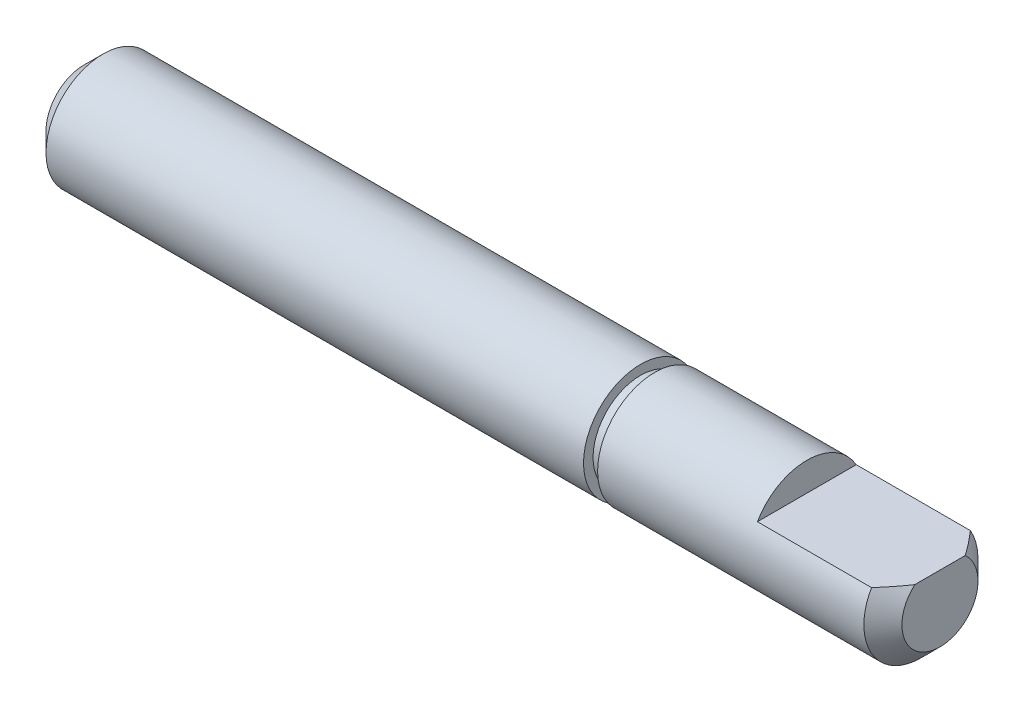
SolidWorks part; units mm, degrees
ref_plane "Plan de face" through (0, 0, 0) normal (0, 0, 1) x (1, 0, 0)
ref_plane "Plan de dessus" through (0, 0, 0) normal (0, 1, 0) x (1, 0, 0)
ref_plane "Plan de droite" through (0, 0, 0) normal (1, 0, 0) x (0, 0, -1)
sketch "Esquisse1" plane through (0, 0, 0) normal (0, 0, 1) x (1, 0, 0)
  line L0 (-55.9394, 0) -> (121.7945, 0) construction
  line L1 (0, 0) -> (0, 2)
  line L2 (0, 2) -> (1, 3)
  line L3 (1, 3) -> (29.26, 3)
  line L4 (29.26, 3) -> (29.26, 2.5)
  line L5 (29.26, 2.5) -> (30, 2.5)
  line L6 (30, 2.5) -> (30, 3)
  line L7 (30, 3) -> (44, 3)
  line L8 (44, 3) -> (45, 2)
  line L9 (45, 2) -> (45, 0)
  line L10 (45, 0) -> (0, 0)
  dimension "D1" = 1
  dimension "D2" = 1
  dimension "D3" = 1
  dimension "D4" = 1
  dimension "D5" = 45
  dimension "D6" = 15
  dimension "D7" = 0.74
  dimension "D8" = 5
  dimension "D9" = 6
  dimension "D10" = 6
revolve "Révolution1" add sketch "Esquisse1" angle 360 about L0
sketch "Esquisse2" plane through (45, 0, 0) normal (1, 0, 0) x (0, 0, -1)
  line L1 (-3.8764, 4.2614) -> (3.3333, 4.2614)
  line L2 (-3.8764, 4.2614) -> (-3.8764, 1.5)
  line L3 (-3.8764, 1.5) -> (3.3333, 1.5)
  line L4 (3.3333, 4.2614) -> (3.3333, 1.5)
  dimension "D1" = 1.5
extrude "Enlèv. mat.-Extru.1" cut sketch "Esquisse2" against normal blind 7
